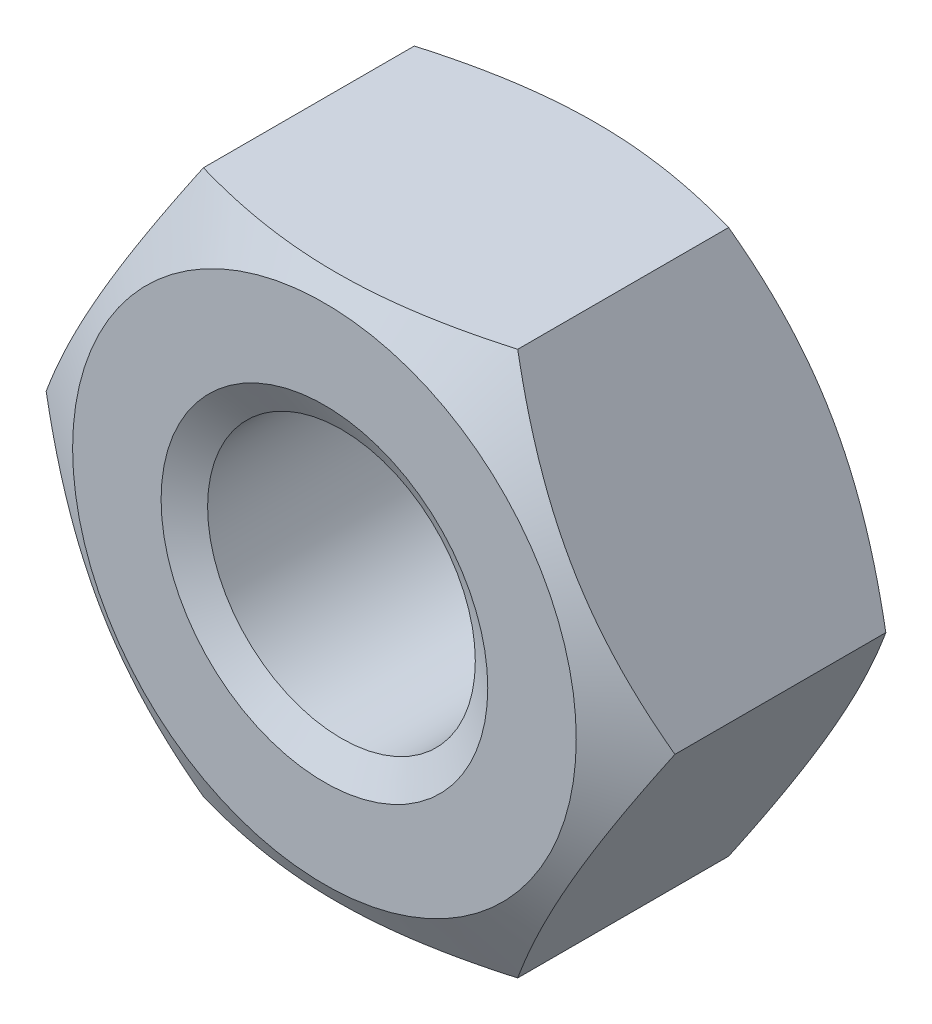
SolidWorks part; units mm, degrees
ref_plane "Front" through (0, 0, 0) normal (0, 0, 1) x (1, 0, 0)
ref_plane "Top" through (0, 0, 0) normal (0, 1, 0) x (1, 0, 0)
ref_plane "Right" through (0, 0, 0) normal (1, 0, 0) x (0, 0, -1)
sketch "Sketch1" plane through (0, 0, 0) normal (0, 0, 1) x (1, 0, 0)
  line L1 (5.7735, 0) -> (2.8868, 5)
  line L2 (2.8868, 5) -> (-2.8868, 5)
  line L3 (-2.8868, 5) -> (-5.7735, 0)
  line L4 (-5.7735, 0) -> (-2.8868, -5)
  line L5 (-2.8868, -5) -> (2.8868, -5)
  line L6 (2.8868, -5) -> (5.7735, 0)
  circle A0 centre (0, 0) radius 5 construction
  circle A1 centre (0, 0) radius 2.4585
  dimension "D" = 4.917
  dimension "s" = 10
extrude "BaseNut" add sketch "Sketch1" against normal blind 5.2
cosmetic thread "ThreadCosmetic1" parameters "D"=6
sketch "Sketch2" plane through (0, 0, 0) normal (0, 1, 0) x (1, 0, 0)
  line L0 (-5.7735, 5.2) -> (-4.625, 5.2)
  line L2 (-4.625, 5.2) -> (-5.7735, 4.5369)
  line L3 (-5.7735, 4.5369) -> (-5.7735, 5.2)
  line L4 (0, 3.3759) -> (0, -9.8171) construction
  line L6 (-9.7712, 2.6) -> (9.8853, 2.6) construction
  line L7 (-5.7735, 0.6631) -> (-5.7735, 0)
  line L8 (-4.625, 0) -> (-5.7735, 0.6631)
  line L9 (-5.7735, 0) -> (-4.625, 0)
  dimension "dw" = 9.25
  dimension "D1" = 30
  dimension "D2" = 2.6
revolve "Double-Chamfer" cut sketch "Sketch2" angle 360 about L4
chamfer "EndChamfer" distance 0.5415 angle 30 2 edges at (2.4585, 0, -5.2) (2.4585, 0, 0)
sketch "Sketch3" plane through (0, 0, 0) normal (0, 1, 0) x (1, 0, 0)
  line L0 (-2.9275, 4.6585) -> (-2.4585, 4.3877)
  line L1 (-2.4585, 4.3877) -> (-1.917, 4.3877)
  line L2 (-1.917, 4.3877) -> (-1.917, 4.9292)
  line L3 (-1.917, 4.9292) -> (-2.4585, 4.9292)
  line L4 (-2.4585, 4.9292) -> (-2.9275, 4.6585)
  line L5 (0, 7.4383) -> (0, 16.8806) construction
  dimension "D1" = 0.5415
  dimension "D2" = 4.917
revolve "Cut-Revolve10" [suppressed] cut sketch "Sketch3" angle 360 about L5
pattern_linear "LPattern10" [suppressed] count 8 spacing 0.6498 along (0, 0, -1)
equation "\"dw@Sketch2\" = \"s@Sketch1\"-0.75"
equation "\"D2@Sketch2\" = \"m@BaseNut\" / 2"
equation "\"D2@Sketch3\" = \"D@Sketch1\""
equation "\"D1@Sketch3\" =  (\"D@ThreadCosmetic1\"   - \"D@Sketch1\")  / 2"
equation "\"D3@LPattern10\" = \"D1@Sketch3\" * 1.2"
equation "\"D1@LPattern10\" = \"m@BaseNut\"/\"D3@LPattern10\""
